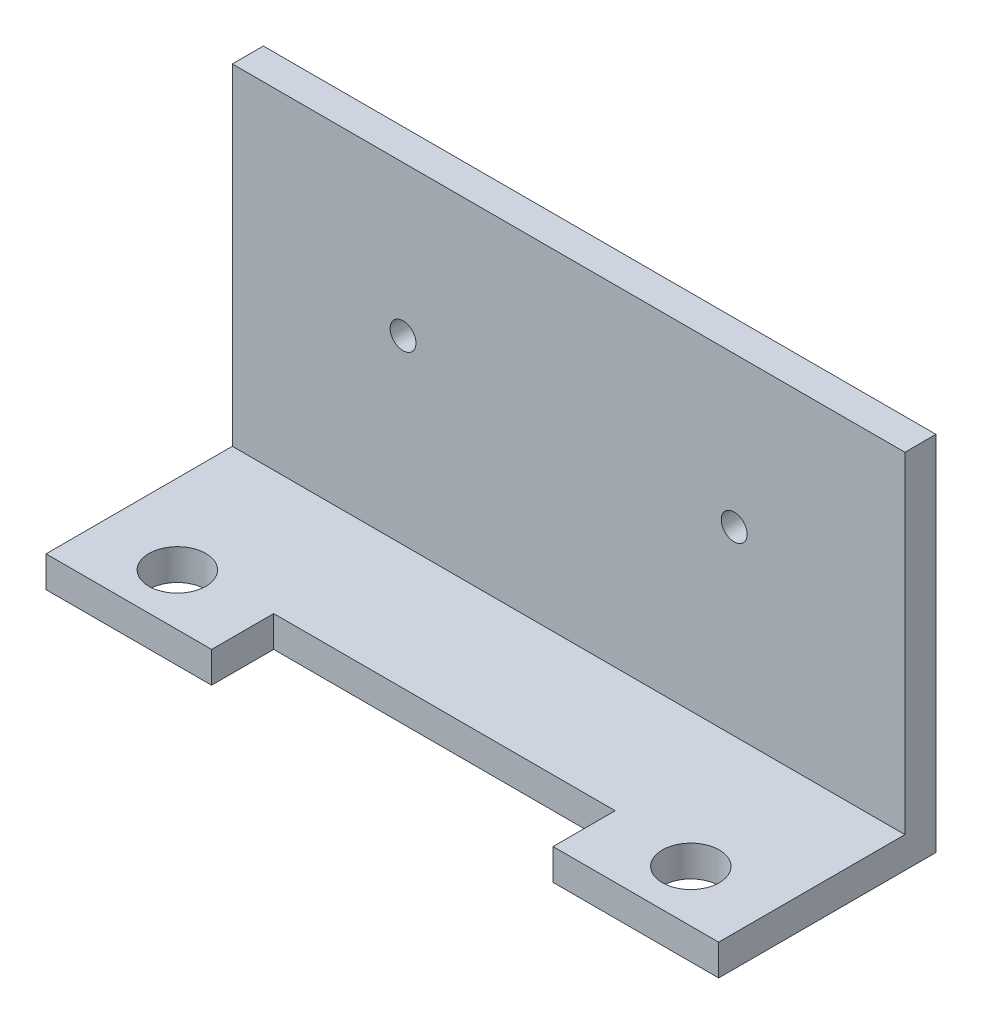
SolidWorks part; units mm, degrees
ref_plane "Front Plane" through (0, 0, 0) normal (0, 0, 1) x (1, 0, 0)
ref_plane "Top Plane" through (0, 0, 0) normal (0, 1, 0) x (1, 0, 0)
ref_plane "Right Plane" through (0, 0, 0) normal (1, 0, 0) x (0, 0, -1)
sketch "Sketch1" plane through (0, 0, 0) normal (0, 1, 0) x (1, 0, 0)
  line L0 (0, 0) -> (16, 0)
  line L5 (16, 0) -> (16, 6)
  line L6 (16, 6) -> (49, 6)
  line L7 (49, 6) -> (49, 0)
  line L8 (49, 0) -> (65, 0)
  line L9 (65, 0) -> (65, 18)
  line L10 (65, 18) -> (0, 18)
  line L11 (0, 18) -> (0, 0)
  circle A0 centre (7.69, 5) radius 2.75
  circle A1 centre (57.31, 5) radius 2.75
  dimension "D4" = 5.5
  dimension "D6" = 13
  dimension "D7" = 7.69
  dimension "D1" = 18
  dimension "D2" = 65
  dimension "D3" = 16
  dimension "D5" = 12
  dimension "D8" = 7.69
  dimension "D9" = 13
extrude "Boss-Extrude1" add sketch "Sketch1" along normal blind 3
sketch "Sketch2" plane through (0, 0, 0) normal (0, 1, 0) x (1, 0, 0)
  line L1 (0, 18) -> (65, 18)
  line L2 (0, 18) -> (0, 21)
  line L3 (0, 21) -> (65, 21)
  line L4 (65, 18) -> (65, 21)
  dimension "D1" = 65
  dimension "D2" = 3
extrude "Boss-Extrude2" add sketch "Sketch2" along normal blind 35
sketch "Sketch3" plane through (0, 0, -18) normal (0, 0, 1) x (1, 0, 0)
  line L0 (0, 35) -> (0, 3) construction
  line L1 (65, 3) -> (0, 3) construction
  circle A0 centre (16.5, 20.5) radius 1.25
  circle A1 centre (48.5, 20.5) radius 1.25
  dimension "D1" = 2.5
  dimension "D2" = 2.5
  dimension "D3" = 32
  dimension "D4" = 16.5
  dimension "D5" = 17.5
extrude "Cut-Extrude1" cut sketch "Sketch3" against normal through all
